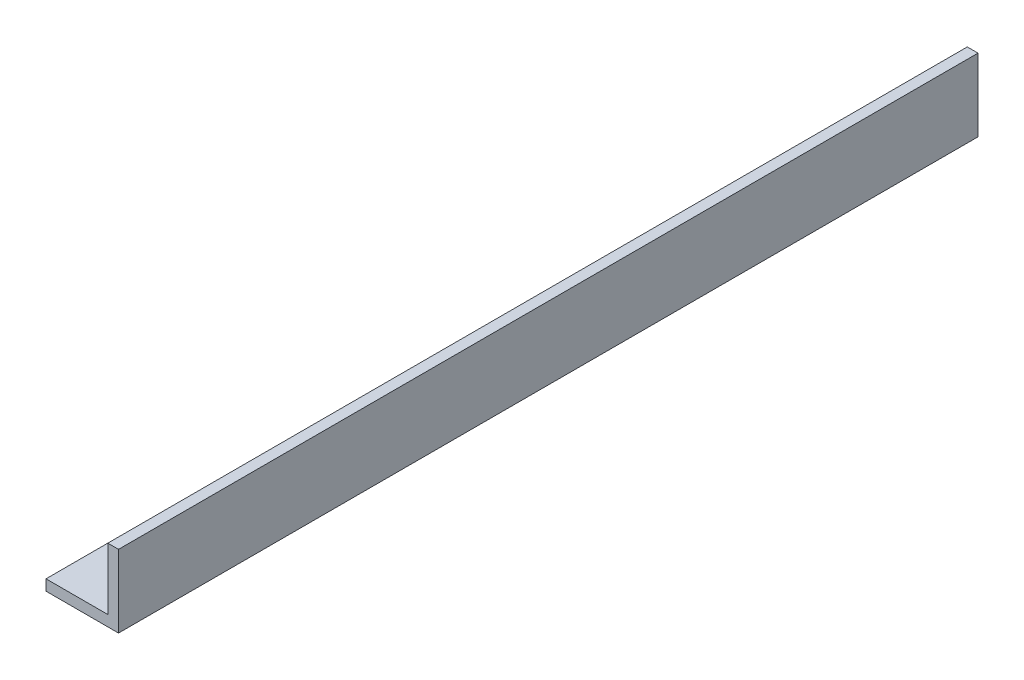
SolidWorks part; units mm, degrees
material "6061 Alloy"
ref_plane "Front" through (0, 0, 0) normal (0, 0, 1) x (1, 0, 0)
ref_plane "Top" through (0, 0, 0) normal (0, 1, 0) x (1, 0, 0)
ref_plane "Right" through (0, 0, 0) normal (1, 0, 0) x (0, 0, -1)
sketch "Sketch1" plane through (0, 0, 0) normal (0, 0, 1) x (1, 0, 0)
  line L0 (0, 0) -> (27, 0)
  line L1 (27, 0) -> (27, 27)
  line L2 (0, 4) -> (23, 4)
  line L3 (23, 4) -> (23, 27)
  line L4 (23, 27) -> (27, 27)
  line L5 (0, 4) -> (0, 0)
  dimension "D1" = 27
  dimension "D2" = 4
extrude "Boss-Extrude1" add sketch "Sketch1" along normal blind 320
